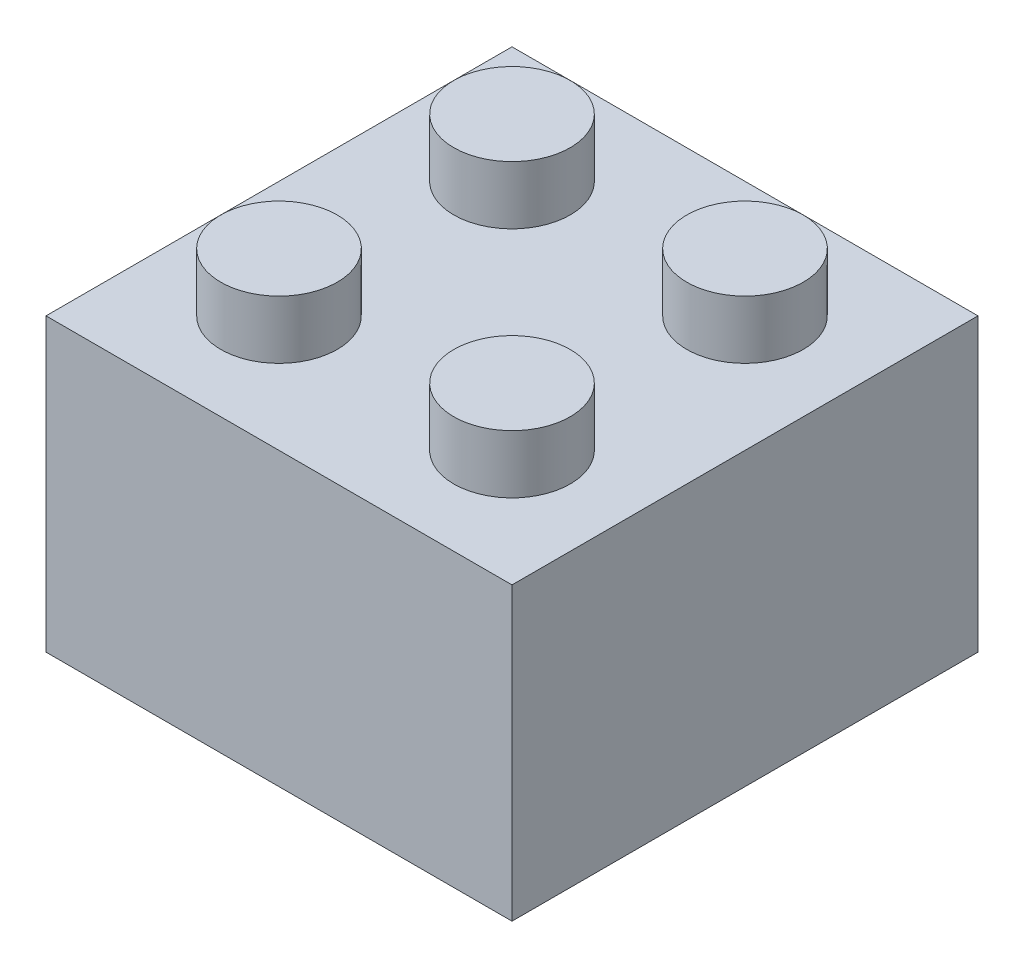
SolidWorks part; units mm, degrees
ref_plane "Front Plane" through (0, 0, 0) normal (0, 0, 1) x (1, 0, 0)
ref_plane "Top Plane" through (0, 0, 0) normal (0, 1, 0) x (1, 0, 0)
ref_plane "Right Plane" through (0, 0, 0) normal (1, 0, 0) x (0, 0, -1)
sketch "Sketch2" plane through (0, 0, 0) normal (0, 1, 0) x (1, 0, 0)
  line L1 (-8, 8) -> (8, 8)
  line L2 (-8, 8) -> (-8, -8)
  line L3 (-8, -8) -> (8, -8)
  line L4 (8, 8) -> (8, -8)
  line L5 (-8, 8) -> (8, -8) construction
  line L6 (-8, -8) -> (8, 8) construction
  point P0 (0, 0)
  dimension "D1" = 16
  dimension "D2" = 16
extrude "Boss-Extrude1" add sketch "Sketch2" along normal blind 10
sketch "Sketch3" plane through (0, 10, 0) normal (0, 1, 0) x (1, 0, 0)
  line L0 (8.9208, 0) -> (0, 0) construction
  line L1 (0, 0) -> (0, 8.6882) construction
  line L2 (-8, 8) -> (-8, -8) construction
  line L3 (8, 8) -> (-8, 8) construction
  circle A0 centre (-4, 4) radius 2
  circle A1 centre (4, 4) radius 2
  circle A2 centre (4, -4) radius 2
  circle A3 centre (-4, -4) radius 2
  dimension "D1" = 4
  dimension "D2" = 4
  dimension "D3" = 4
extrude "Boss-Extrude2" add sketch "Sketch3" along normal blind 2
shell "Shell2" thickness 1
sketch "Sketch4" plane through (0, 9, 0) normal (0, -1, 0) x (1, 0, 0)
  circle A0 centre (0, 0) radius 1.7
  circle A1 centre (0, 0) radius 2.7
  dimension "D1" = 5.4
  dimension "D2" = 3.4
extrude "Boss-Extrude3" add sketch "Sketch4" along normal blind 9
